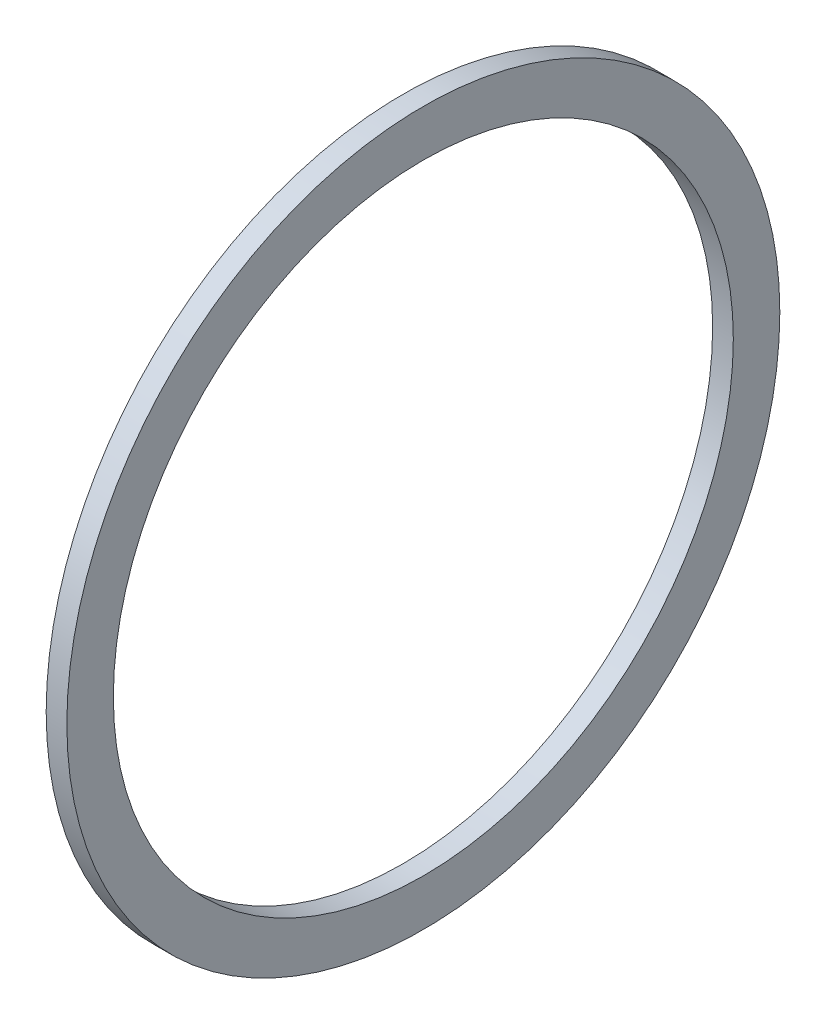
SolidWorks part; units mm, degrees
ref_plane "Plan de face" through (0, 0, 0) normal (1, 0, 0) x (0, 1, 0)
ref_plane "Plan de dessus" through (0, 0, 0) normal (0, 0, 1) x (0, 1, 0)
ref_plane "Plan de droite" through (0, 0, 0) normal (0, 1, 0) x (-1, 0, 0)
sketch "Esquisse1" plane through (0, 0, 0) normal (1, 0, 0) x (0, 1, 0)
  circle A0 centre (0, 0) radius 34.5
  circle A1 centre (0, 0) radius 30
  dimension "D1" = 69
  dimension "D2" = 60
extrude "Boss.-Extru.1" add sketch "Esquisse1" along normal blind 2
